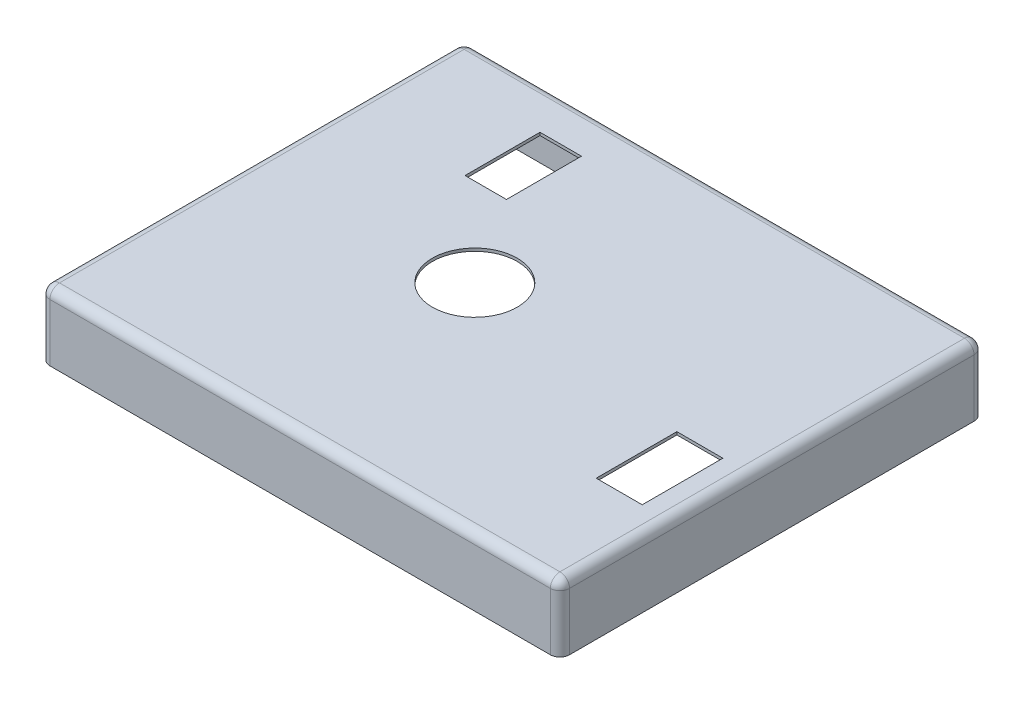
SolidWorks part; units mm, degrees
ref_plane "Plan de face" through (0, 0, 0) normal (0, 0, 1) x (1, 0, 0)
ref_plane "Plan de dessus" through (0, 0, 0) normal (0, 1, 0) x (1, 0, 0)
ref_plane "Plan de droite" through (0, 0, 0) normal (1, 0, 0) x (0, 0, -1)
sketch "Esquisse3" plane through (0, 0, 0) normal (0, 1, 0) x (1, 0, 0)
  line L0 (0, -17.5274) -> (0, 20.5834) construction
  line L2 (-26.5045, 19.9542) -> (25.6955, 19.9542)
  line L3 (-27.5045, 18.9542) -> (-27.5045, -23.2458)
  line L4 (-26.5045, -24.2458) -> (25.6955, -24.2458)
  line L5 (26.6955, 18.9542) -> (26.6955, -23.2458)
  arc A0 (25.6955, 19.9542) -> (26.6955, 18.9542) centre (25.6955, 18.9542) cw
  arc A1 (26.6955, -23.2458) -> (25.6955, -24.2458) centre (25.6955, -23.2458) cw
  arc A2 (-26.5045, -24.2458) -> (-27.5045, -23.2458) centre (-26.5045, -23.2458) cw
  arc A3 (-27.5045, 18.9542) -> (-26.5045, 19.9542) centre (-26.5045, 18.9542) cw
  point P7 (0, 0)
  point P8 (0, 0)
  point P9 (-27.2348, 21.0328)
  point P12 (26.6955, 19.9542)
  point P17 (-27.5045, -24.2458)
  point P20 (-27.5045, 19.9542)
  dimension "D2" = 1
  dimension "D1" = 54.2
  dimension "44.2" = 44.2
extrude "Boss.-Extru.1" add sketch "Esquisse3" along normal blind 7 contours L3 A2 L4 A1 L5 A0 L2 A3
fillet "Congé1" radius 1 8 edges at (26.4026, 7, -19.6613) (-27.2116, 7, -19.6613) (26.4026, 7, 23.9529) (-0.4045, 7, 24.2458) (-27.2116, 7, 23.9529) (26.6955, 7, 2.1458) (-0.4045, 7, -19.9542) (-27.5045, 7, 2.1458)
shell "Coque1" thickness 0.3
sketch "Esquisse8" plane through (0, 7, 0) normal (0, 1, 0) x (1, 0, 0)
  circle A0 centre (-4.8655, -1.5646) radius 4.428
extrude "Enlèv. mat.-Extru.1" cut sketch "Esquisse8" against normal up to next
sketch "Esquisse9" plane through (0, 7, 0) normal (0, 1, 0) x (1, 0, 0)
  line L1 (-15.0538, 15.4241) -> (-10.7286, 15.4241)
  line L2 (-15.0538, 15.4241) -> (-15.0538, 7.6032)
  line L3 (-15.0538, 7.6032) -> (-10.7286, 7.6032)
  line L4 (-10.7286, 15.4241) -> (-10.7286, 7.6032)
extrude "Enlèv. mat.-Extru.2" cut sketch "Esquisse9" against normal up to next
sketch "Esquisse10" plane through (0, 7, 0) normal (0, 1, 0) x (1, 0, 0)
  line L1 (19.1331, -4.4837) -> (23.9323, -4.4837)
  line L2 (19.1331, -4.4837) -> (19.1331, -12.8971)
  line L3 (19.1331, -12.8971) -> (23.9323, -12.8971)
  line L4 (23.9323, -4.4837) -> (23.9323, -12.8971)
extrude "Enlèv. mat.-Extru.3" cut sketch "Esquisse10" against normal up to next
